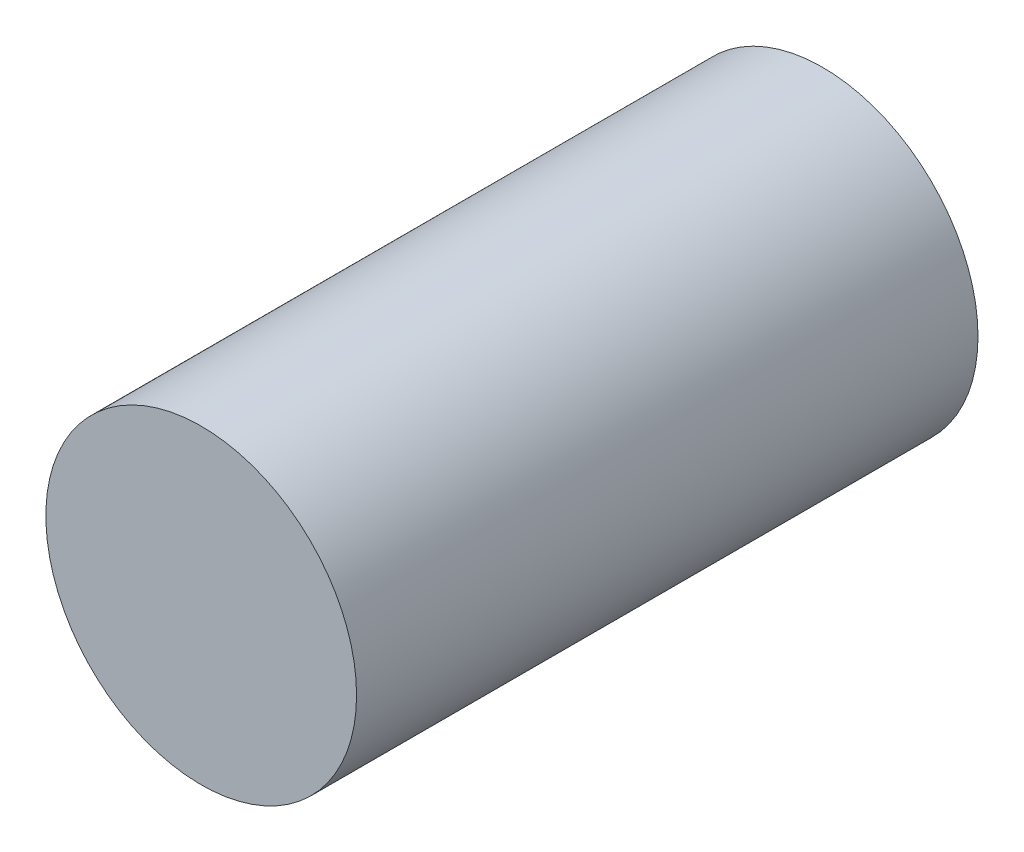
SolidWorks part; units mm, degrees
ref_plane "Alzado" through (0, 0, 0) normal (0, 0, 1) x (1, 0, 0)
ref_plane "Planta" through (0, 0, 0) normal (0, 1, 0) x (1, 0, 0)
ref_plane "Vista lateral" through (0, 0, 0) normal (1, 0, 0) x (0, 0, -1)
sketch "Sketch1" plane through (0, 0, 0) normal (0, 0, 1) x (1, 0, 0)
  circle A0 centre (0, 0) radius 2.5
extrude "Boss-Extrude1" add sketch "Sketch1" along normal blind 10
